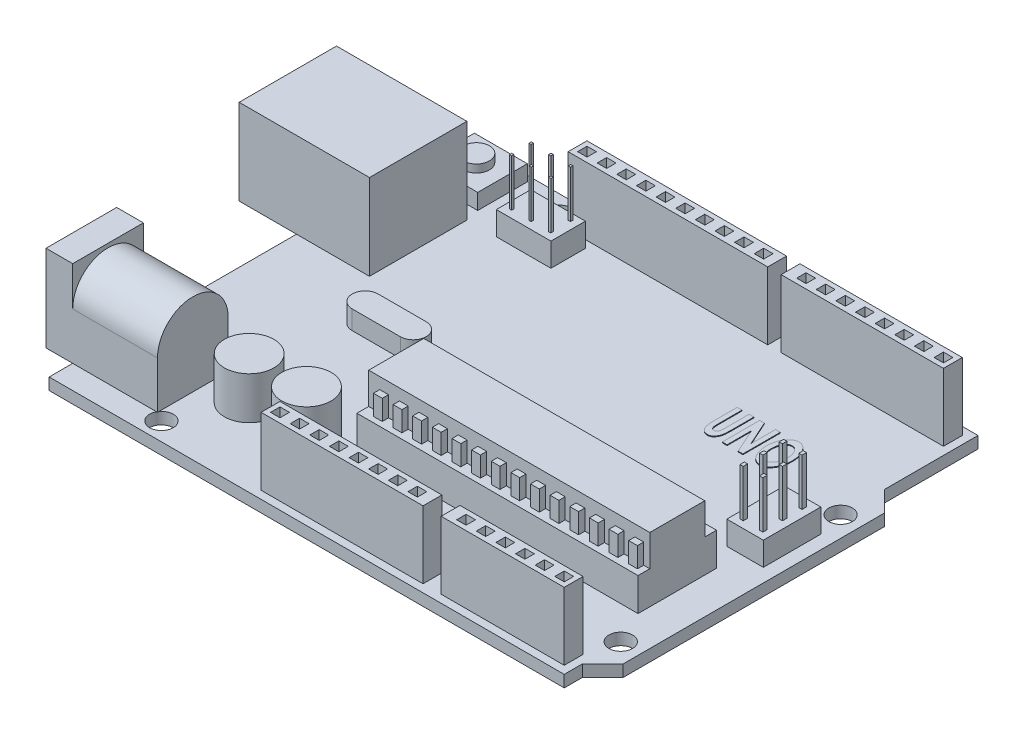
SolidWorks part; units mm, degrees
ref_plane "前基準面" through (0, 0, 0) normal (0, 0, 1) x (1, 0, 0)
ref_plane "上基準面" through (0, 0, 0) normal (0, 1, 0) x (1, 0, 0)
ref_plane "右基準面" through (0, 0, 0) normal (1, 0, 0) x (0, 0, -1)
sketch "草圖1" plane through (0, 0, 0) normal (0, 1, 0) x (1, 0, 0)
  line L0 (25.2641, 24.6244) -> (27.8641, 22.0244)
  line L1 (-40.3359, 36.5244) -> (25.2641, 36.5244)
  line L2 (-40.3359, 36.5244) -> (-40.3359, -16.1756)
  line L3 (-40.3359, -16.1756) -> (25.2641, -16.1756)
  line L4 (25.2641, 36.5244) -> (25.2641, 24.6244)
  line L5 (27.8641, 22.0244) -> (27.8641, -11.2756)
  line L6 (27.8641, -11.2756) -> (25.2641, -13.8756)
  line L7 (25.2641, -13.8756) -> (25.2641, -16.1756)
  line L8 (25.2641, 19.0244) -> (25.2641, -8.9756) construction
  line L9 (-7.5359, 36.5244) -> (-7.5359, -16.1756) construction
  circle A0 centre (25.2641, 19.0244) radius 1.5
  circle A1 centre (25.2641, -8.9756) radius 1.5
  circle A2 centre (-25.7359, 34.2244) radius 1.5
  circle A3 centre (-28.3359, -13.8756) radius 1.5
  dimension "D8" = 3
  dimension "D9" = 3
  dimension "D10" = 1.1
  dimension "D12" = 16
  dimension "D13" = 0.8
  dimension "D14" = 0.8
  dimension "D15" = 13.1
  dimension "D16" = 3
  dimension "D17" = 12
  dimension "D18" = 3
  dimension "D1" = 52.7
  dimension "D2" = 65.6
  dimension "D3" = 2.6
  dimension "D4" = 2.3
  dimension "D5" = 135
  dimension "D6" = 11.9
  dimension "D7" = 135
  dimension "D11" = 28
extrude "填料-伸長1" add sketch "草圖1" along normal blind 1.5
sketch "草圖2" plane through (0, 1.5, 0) normal (0, 1, 0) x (1, 0, 0)
  line L0 (-40.3359, 36.5244) -> (-40.3359, -16.1756) construction
  line L1 (-47.6359, 27.7244) -> (-31.0359, 27.7244)
  line L2 (-47.6359, 27.7244) -> (-47.6359, 15.3244)
  line L3 (-47.6359, 15.3244) -> (-31.0359, 15.3244)
  line L4 (-31.0359, 27.7244) -> (-31.0359, 15.3244)
  line L5 (25.2641, 36.5244) -> (-40.3359, 36.5244) construction
  dimension "D1" = 16.6
  dimension "D2" = 12.4
  dimension "D3" = 7.3
  dimension "D4" = 8.8
extrude "填料-伸長2" add sketch "草圖2" along normal blind 10.9
sketch "草圖3" plane through (-47.6359, 0, 0) normal (-1, 0, 0) x (0, 0, 1)
  line L0 (-24.4011, 11.3216) -> (-18.6505, 11.3216)
  line L1 (-23.7422, 8.3265) -> (-19.3694, 8.3265)
  line L2 (-23.7422, 8.3265) -> (-23.7422, 6.2899)
  line L3 (-23.7422, 6.2899) -> (-19.3694, 6.2899)
  line L4 (-19.3694, 8.3265) -> (-19.3694, 6.2899)
  line L5 (-18.6505, 11.3216) -> (-16.4042, 9.0753)
  line L6 (-16.4042, 9.0753) -> (-16.4042, 2.8155)
  line L7 (-16.4042, 2.8155) -> (-26.6774, 2.8155)
  line L8 (-26.6774, 2.8155) -> (-26.6774, 9.0753)
  line L9 (-26.6774, 9.0753) -> (-24.4011, 11.3216)
extrude "除料-伸長1" cut sketch "草圖3" against normal blind 10.9
sketch "草圖4" plane through (0, 1.5, 0) normal (0, 1, 0) x (1, 0, 0)
  line L1 (-38.148, 35.7984) -> (-31.4042, 35.7984)
  line L2 (-38.148, 35.7984) -> (-38.148, 29.4753)
  line L3 (-38.148, 29.4753) -> (-31.4042, 29.4753)
  line L4 (-31.4042, 35.7984) -> (-31.4042, 29.4753)
extrude "填料-伸長3" add sketch "草圖4" along normal blind 2
sketch "草圖5" plane through (0, 3.5, 0) normal (0, 1, 0) x (1, 0, 0)
  circle A0 centre (-34.7975, 32.6949) radius 1.6646
extrude "填料-伸長4" add sketch "草圖5" along normal blind 1
sketch "草圖6" plane through (0, 1.5, 0) normal (0, 1, 0) x (1, 0, 0)
  line L0 (25.2641, 36.5244) -> (-40.3359, 36.5244) construction
  line L1 (-23.5359, 35.5244) -> (24.2641, 35.5244)
  line L2 (-23.5359, 35.5244) -> (-23.5359, 33.1244)
  line L3 (-23.5359, 33.1244) -> (24.2641, 33.1244)
  line L4 (24.2641, 35.5244) -> (24.2641, 33.1244)
  line L5 (25.2641, 24.6244) -> (25.2641, 36.5244) construction
  line L6 (25.2641, -16.1756) -> (25.2641, -13.8756) construction
  line L7 (24.2641, -15.1756) -> (-14.3359, -15.1756)
  line L8 (24.2641, -15.1756) -> (24.2641, -12.7756)
  line L9 (24.2641, -12.7756) -> (-14.3359, -12.7756)
  line L10 (-14.3359, -15.1756) -> (-14.3359, -12.7756)
  line L11 (-40.3359, -16.1756) -> (25.2641, -16.1756) construction
  dimension "D1" = 47.8
  dimension "D2" = 2.4
  dimension "D3" = 1
  dimension "D4" = 1
  dimension "D5" = 2.4
  dimension "D6" = 38.6
  dimension "D7" = 1
  dimension "D8" = 1
extrude "填料-伸長5" add sketch "草圖6" along normal blind 8.6
sketch "草圖7" plane through (0, 1.5, 0) normal (0, 1, 0) x (1, 0, 0)
  line L0 (27.8641, -11.2756) -> (27.8641, 22.0244) construction
  line L1 (-12.5359, 5.2244) -> (23.2641, 5.2244)
  line L2 (-12.5359, 5.2244) -> (-12.5359, -4.7756)
  line L3 (-12.5359, -4.7756) -> (23.2641, -4.7756)
  line L4 (23.2641, 5.2244) -> (23.2641, -4.7756)
  line L5 (24.2641, -12.7756) -> (-14.3359, -12.7756) construction
  dimension "D1" = 4.6
  dimension "D2" = 10
  dimension "D3" = 35.8
  dimension "D4" = 8
extrude "填料-伸長6" add sketch "草圖7" along normal blind 8.2
sketch "草圖8" plane through (0, 1.5, 0) normal (0, 1, 0) x (1, 0, 0)
  line L0 (-24.7753, -6.2598) -> (-17.4808, -6.2598) construction
  line L1 (-26.1439, 9.8798) -> (-20.0177, 9.8798) construction
  line L2 (-26.1439, 11.5292) -> (-20.0177, 11.5292)
  line L3 (-26.1439, 8.2305) -> (-20.0177, 8.2305)
  circle A0 centre (-24.7753, -6.2598) radius 3.15
  circle A1 centre (-17.4808, -6.2598) radius 3.15
  arc A2 (-26.1439, 11.5292) -> (-26.1439, 8.2305) centre (-26.1439, 9.8798) ccw
  arc A3 (-20.0177, 8.2305) -> (-20.0177, 11.5292) centre (-20.0177, 9.8798) ccw
  point P6 (-23.0808, 9.8798)
  dimension "D1" = 6.3
  dimension "D2" = 6.3
extrude "填料-伸長7" add sketch "草圖8" along normal blind 5.4
sketch "草圖9" plane through (0, 10.1, 0) normal (0, 1, 0) x (1, 0, 0)
  line L0 (-23.5359, 33.1244) -> (24.2641, 33.1244) construction
  line L1 (23.6641, 34.9244) -> (22.4641, 34.9244)
  line L2 (23.6641, 34.9244) -> (23.6641, 33.7244)
  line L3 (23.6641, 33.7244) -> (22.4641, 33.7244)
  line L4 (22.4641, 34.9244) -> (22.4641, 33.7244)
  line L5 (24.2641, 33.1244) -> (24.2641, 35.5244) construction
  dimension "D1" = 1.2
  dimension "D2" = 1.2
  dimension "D3" = 0.6
  dimension "D4" = 0.6
extrude "除料-伸長2" cut sketch "草圖9" against normal blind 5.4
pattern_linear "直線複製排列1" count 8 spacing 2.5 along (-1, 0, 0) of "除料-伸長2"
sketch "草圖10" plane through (0, 10.1, 0) normal (0, 1, 0) x (1, 0, 0)
  line L0 (-23.5359, 33.1244) -> (24.2641, 33.1244) construction
  line L1 (-22.9359, 34.9244) -> (-21.7359, 34.9244)
  line L2 (-22.9359, 34.9244) -> (-22.9359, 33.7244)
  line L3 (-22.9359, 33.7244) -> (-21.7359, 33.7244)
  line L4 (-21.7359, 34.9244) -> (-21.7359, 33.7244)
  line L5 (-23.5359, 35.5244) -> (-23.5359, 33.1244) construction
  dimension "D1" = 1.2
  dimension "D2" = 1.2
  dimension "D3" = 0.6
  dimension "D4" = 0.6
extrude "除料-伸長3" cut sketch "草圖10" against normal blind 5.4
pattern_linear "直線複製排列2" count 10 spacing 2.5 along (1, 0, 0) of "除料-伸長3"
sketch "草圖11" plane through (0, 10.1, 0) normal (0, 1, 0) x (1, 0, 0)
  line L0 (-14.3359, -15.1756) -> (24.2641, -15.1756) construction
  line L1 (23.6641, -13.3756) -> (22.4641, -13.3756)
  line L2 (23.6641, -13.3756) -> (23.6641, -14.5756)
  line L3 (23.6641, -14.5756) -> (22.4641, -14.5756)
  line L4 (22.4641, -13.3756) -> (22.4641, -14.5756)
  line L5 (24.2641, -15.1756) -> (24.2641, -12.7756) construction
  dimension "D1" = 1.2
  dimension "D2" = 1.2
  dimension "D3" = 0.6
  dimension "D4" = 0.6
extrude "除料-伸長4" cut sketch "草圖11" against normal blind 5.4
pattern_linear "直線複製排列3" count 6 spacing 2.5 along (-1, 0, 0) of "除料-伸長4"
sketch "草圖12" plane through (0, 10.1, 0) normal (0, 1, 0) x (1, 0, 0)
  line L0 (-14.3359, -15.1756) -> (24.2641, -15.1756) construction
  line L1 (-13.7359, -13.3756) -> (-12.5359, -13.3756)
  line L2 (-13.7359, -13.3756) -> (-13.7359, -14.5756)
  line L3 (-13.7359, -14.5756) -> (-12.5359, -14.5756)
  line L4 (-12.5359, -13.3756) -> (-12.5359, -14.5756)
  line L5 (-14.3359, -12.7756) -> (-14.3359, -15.1756) construction
  dimension "D1" = 1.2
  dimension "D2" = 1.2
  dimension "D3" = 0.6
  dimension "D4" = 0.6
extrude "除料-伸長5" cut sketch "草圖12" against normal blind 5.4
pattern_linear "直線複製排列4" count 8 spacing 2.5 along (1, 0, 0) of "除料-伸長5"
sketch "草圖13" plane through (-40.3359, 0, 0) normal (-1, 0, 0) x (0, 0, 1)
  line L0 (-15.3244, 1.5) -> (16.1756, 1.5) construction
  line L1 (13.1756, 1.5) -> (4.1756, 1.5)
  line L2 (13.1756, 1.5) -> (13.1756, 12.5)
  line L3 (13.1756, 12.5) -> (4.1756, 12.5)
  line L4 (4.1756, 1.5) -> (4.1756, 12.5)
  line L5 (16.1756, 1.5) -> (16.1756, 0) construction
  dimension "D1" = 11
  dimension "D2" = 9
  dimension "D3" = 3
extrude "填料-伸長8" add sketch "草圖13" along normal blind 3.4 separate body
sketch "草圖14" plane through (-40.3359, 0, 0) normal (1, 0, 0) x (0, 0, -1)
  line L0 (-13.1756, 7.5) -> (-13.1756, 1.5)
  line L1 (-4.1756, 1.5) -> (-13.1756, 1.5) construction
  line L2 (-13.1756, 1.5) -> (-4.1756, 1.5)
  line L3 (-11.2756, 1.5) -> (22.0244, 1.5) construction
  line L4 (-4.1756, 1.5) -> (-4.1756, 7.5)
  line L5 (-13.1756, 1.5) -> (-13.1756, 12.5) construction
  line L6 (15.3244, 1.5) -> (-16.1756, 1.5) construction
  arc A0 (-4.1756, 7.5) -> (-13.1756, 7.5) centre (-8.6756, 7.5) ccw
  dimension "D1" = 4.5
  dimension "D2" = 6
extrude "填料-伸長9" add sketch "草圖14" along normal blind 10.8
sketch "草圖15" plane through (-43.7359, 0, 0) normal (-1, 0, 0) x (0, 0, 1)
  circle A0 centre (8.6756, 7.5) radius 3.8845
  circle A1 centre (8.6756, 7.5) radius 0.4076
extrude "除料-伸長6" cut sketch "草圖15" against normal blind 10.8
sketch "草圖16" plane through (0, 9.7, 0) normal (0, 1, 0) x (1, 0, 0)
  line L0 (23.2641, -4.7756) -> (23.2641, 5.2244) construction
  line L1 (-12.5359, 5.2244) -> (23.2641, 5.2244)
  line L2 (-12.5359, 5.2244) -> (-12.5359, 3.7244)
  line L3 (-12.5359, 3.7244) -> (23.2641, 3.7244)
  line L4 (23.2641, 5.2244) -> (23.2641, 3.7244)
  line L6 (-12.5359, -4.7756) -> (23.2641, -4.7756)
  line L7 (-12.5359, -4.7756) -> (-12.5359, -3.2756)
  line L8 (-12.5359, -3.2756) -> (23.2641, -3.2756)
  line L9 (23.2641, -4.7756) -> (23.2641, -3.2756)
  dimension "D1" = 1.5
  dimension "D2" = 1.5
extrude "除料-伸長7" cut sketch "草圖16" against normal blind 4
sketch "草圖17" plane through (0, 0, 3.2756) normal (0, 0, 1) x (1, 0, 0)
  line L0 (23.2641, 5.7) -> (-12.5359, 5.7) construction
  line L1 (21.3731, 8.261) -> (22.4916, 8.261)
  line L2 (21.3731, 8.261) -> (21.3731, 5.7)
  line L3 (21.3731, 5.7) -> (22.4916, 5.7)
  line L4 (22.4916, 8.261) -> (22.4916, 5.7)
extrude "填料-伸長10" add sketch "草圖17" along normal blind 0.8
pattern_linear "直線複製排列5" count 14 spacing 2.5 along (-1, 0, 0) of "填料-伸長10"
sketch "草圖18" plane through (0, 0, -3.7244) normal (0, 0, -1) x (-1, 0, 0)
  line L1 (-21.3731, 8.261) -> (-22.4916, 8.261)
  line L2 (-21.3731, 8.261) -> (-21.3731, 5.7)
  line L3 (-21.3731, 5.7) -> (-22.4916, 5.7)
  line L4 (-22.4916, 8.261) -> (-22.4916, 5.7)
extrude "填料-伸長11" add sketch "草圖18" along normal blind 0.8
pattern_linear "直線複製排列6" count 14 spacing 2.5 along (-1, 0, 0) of "填料-伸長11"
sketch "草圖19" plane through (0, 10.1, 0) normal (0, 1, 0) x (1, 0, 0)
  line L0 (24.2641, -12.7756) -> (-14.3359, -12.7756) construction
  line L1 (6.287, -12.7756) -> (8.5909, -12.7756)
  line L2 (6.287, -12.7756) -> (6.287, -15.1756)
  line L3 (6.287, -15.1756) -> (8.5909, -15.1756)
  line L4 (8.5909, -12.7756) -> (8.5909, -15.1756)
  line L5 (-14.3359, -15.1756) -> (24.2641, -15.1756) construction
  line L6 (24.2641, 35.5244) -> (-23.5359, 35.5244) construction
  line L7 (1.8829, 35.5244) -> (3.5883, 35.5244)
  line L8 (1.8829, 35.5244) -> (1.8829, 33.1244)
  line L9 (1.8829, 33.1244) -> (3.5883, 33.1244)
  line L10 (3.5883, 35.5244) -> (3.5883, 33.1244)
  line L11 (-23.5359, 33.1244) -> (24.2641, 33.1244) construction
extrude "除料-伸長8" cut sketch "草圖19" against normal up to surface (8.6 mm away) up to face at (-24.7753, 1.5, 9.4098)
sketch "草圖20" plane through (0, 1.5, 0) normal (0, 1, 0) x (1, 0, 0)
  line L1 (26.1424, 15.6221) -> (21.4933, 15.6221)
  line L2 (26.1424, 15.6221) -> (26.1424, 8.3036)
  line L3 (26.1424, 8.3036) -> (21.4933, 8.3036)
  line L4 (21.4933, 15.6221) -> (21.4933, 8.3036)
  line L5 (-27.3258, 32.1564) -> (-20.3705, 32.1564)
  line L6 (-27.3258, 32.1564) -> (-27.3258, 27.7655)
  line L7 (-27.3258, 27.7655) -> (-20.3705, 27.7655)
  line L8 (-20.3705, 32.1564) -> (-20.3705, 27.7655)
extrude "填料-伸長12" add sketch "草圖20" along normal blind 3
sketch "草圖21" plane through (0, 4.5, 0) normal (0, 1, 0) x (1, 0, 0)
  line L1 (22.3105, 14.7152) -> (22.7281, 14.7152)
  line L2 (22.3105, 14.7152) -> (22.3105, 14.1584)
  line L3 (22.3105, 14.1584) -> (22.7281, 14.1584)
  line L4 (22.7281, 14.7152) -> (22.7281, 14.1584)
extrude "填料-伸長13" add sketch "草圖21" along normal blind 6
pattern_linear "直線複製排列7" count 2 spacing 2.5 along (1, 0, 0) count 3 spacing 2.5 along (0, 0, 1) of "填料-伸長13"
sketch "草圖22" plane through (0, 4.5, 0) normal (0, 1, 0) x (1, 0, 0)
  line L1 (-26.5592, 31.4655) -> (-26.2729, 31.4655)
  line L2 (-26.5592, 31.4655) -> (-26.5592, 31.1571)
  line L3 (-26.5592, 31.1571) -> (-26.2729, 31.1571)
  line L4 (-26.2729, 31.4655) -> (-26.2729, 31.1571)
extrude "填料-伸長14" add sketch "草圖22" along normal blind 6
pattern_linear "直線複製排列8" count 3 spacing 2.5 along (1, 0, 0) count 2 spacing 2.5 along (0, 0, 1) of "填料-伸長14"
sketch "草圖23" plane through (0, 6.9, 0) normal (0, 1, 0) x (1, 0, 0)
  line L2 (-26.1439, 8.2305) -> (-20.0177, 8.2305)
  line L3 (-20.0177, 11.5292) -> (-26.1439, 11.5292)
  line L4 (-26.1439, 8.2305) -> (-20.0177, 8.2305)
  line L5 (-20.0177, 11.5292) -> (-26.1439, 11.5292)
  arc A2 (-26.1439, 11.5292) -> (-26.1439, 8.2305) centre (-26.1439, 9.8798) ccw
  arc A3 (-20.0177, 8.2305) -> (-20.0177, 11.5292) centre (-20.0177, 9.8798) ccw
  arc A4 (-26.1439, 11.5292) -> (-26.1439, 8.2305) centre (-26.1439, 9.8798) ccw
  arc A5 (-20.0177, 8.2305) -> (-20.0177, 11.5292) centre (-20.0177, 9.8798) ccw
  dimension "D1" = 0
extrude "除料-伸長9" cut sketch "草圖23" against normal blind 3
sketch "草圖24" plane through (0, 1.5, 0) normal (0, 1, 0) x (1, 0, 0)
  text T0 "<b>UNO</b>" font "Century Gothic" height in points 18
extrude "填料-伸長15" add sketch "草圖24" along normal blind 0.1
